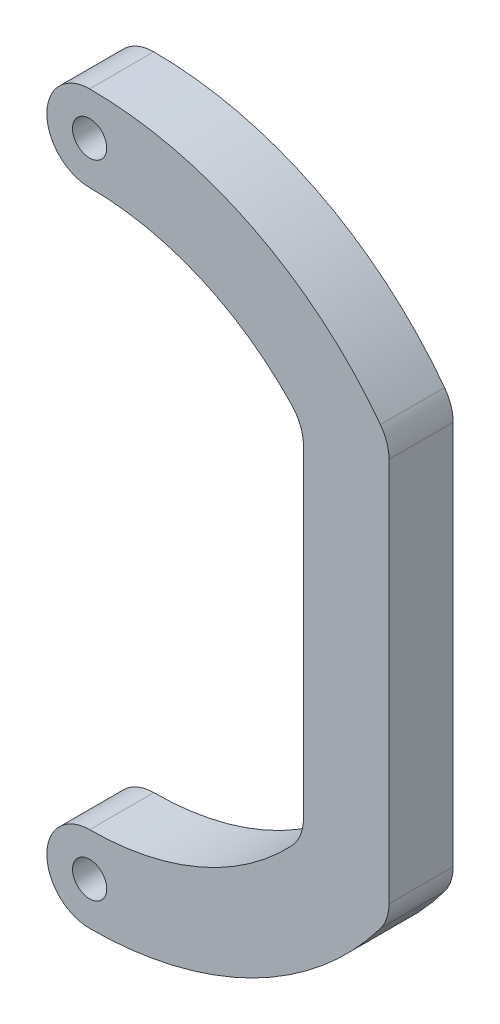
SolidWorks part; units mm, degrees
material "Nichtrostender Chromstahl"
ref_plane "Ebene vorne" through (0, 0, 0) normal (0, 0, 1) x (1, 0, 0)
ref_plane "Ebene oben" through (0, 0, 0) normal (0, 1, 0) x (1, 0, 0)
ref_plane "Ebene rechts" through (0, 0, 0) normal (1, 0, 0) x (0, 0, -1)
sketch "Skizze1" plane through (0, 0, 0) normal (0, 0, 1) x (1, 0, 0)
  line L0 (-75, -142) -> (-75, -18.3969) construction
  line L1 (-25, -29.2508) -> (-25, -104.7492)
  line L3 (-67.8695, -142) -> (-83.3079, -142) construction
  line L4 (-17.5, -67) -> (-147.3228, -67) construction
  line L5 (-5, -22) -> (-5, -112)
  line L6 (-15, -18.3969) -> (-15, -149.859) construction
  line L7 (-5, -18.3969) -> (-5, -149.859) construction
  line L8 (-25, -18.3969) -> (-25, -149.859) construction
  arc A0 (-75, -142) -> (-15, -112) centre (-75, -67) ccw construction
  arc A1 (-75, -152) -> (-7, -118) centre (-75, -67) ccw
  arc A2 (-75, -132) -> (-27.7273, -111.6127) centre (-75, -67) ccw
  arc A3 (-75, -152) -> (-75, -132) centre (-75, -142) cw
  arc A4 (-75, 18) -> (-75, -2) centre (-75, 8) ccw
  circle A5 centre (-75, -142) radius 4
  circle A6 centre (-75, 8) radius 4
  arc A7 (-15, -22) -> (-75, 8) centre (-75, -67) ccw construction
  arc A8 (-75, -142) -> (-75, 8) centre (-75, -67) ccw construction
  arc A9 (-7, -16) -> (-75, 18) centre (-75, -67) ccw
  arc A10 (-75, -152) -> (-75, 18) centre (-75, -67) ccw construction
  arc A11 (-27.7273, -22.3873) -> (-75, -2) centre (-75, -67) ccw
  arc A12 (-75, -132) -> (-75, -2) centre (-75, -67) ccw construction
  arc A13 (-25, -29.2508) -> (-27.7273, -22.3873) centre (-35, -29.2508) ccw
  arc A14 (-7, -16) -> (-5, -22) centre (-15, -22) cw
  arc A15 (-27.7273, -111.6127) -> (-25, -104.7492) centre (-35, -104.7492) ccw
  arc A16 (-7, -118) -> (-5, -112) centre (-15, -112) ccw
  point P32 (-25, -25.4669)
  dimension "D2" = 75
  dimension "D3" = 60
  dimension "D4" = 10
  dimension "D5" = 8
  dimension "D8" = 10
  dimension "D9" = 10
  dimension "D1" = 75
  dimension "D6" = 10
  dimension "D7" = 10
extrude "Linear austragen1" add sketch "Skizze1" along normal blind 15
